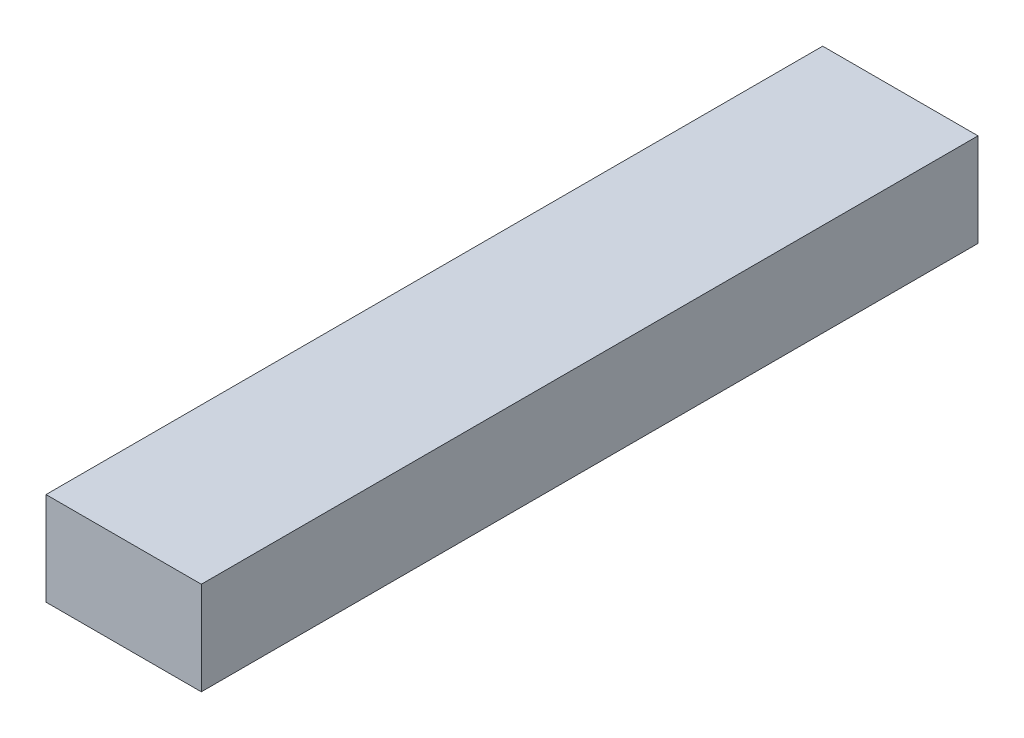
SolidWorks part; units mm, degrees
material "1060-H14"
ref_plane "Front Plane" through (0, 0, 0) normal (0, 0, 1) x (1, 0, 0)
ref_plane "Top Plane" through (0, 0, 0) normal (0, 1, 0) x (1, 0, 0)
ref_plane "Right Plane" through (0, 0, 0) normal (1, 0, 0) x (0, 0, -1)
sketch "Sketch1" plane through (0, 0, 0) normal (0, 1, 0) x (1, 0, 0)
  line L1 (-0.5, -2.5) -> (0.5, -2.5)
  line L2 (-0.5, -2.5) -> (-0.5, 2.5)
  line L3 (-0.5, 2.5) -> (0.5, 2.5)
  line L4 (0.5, -2.5) -> (0.5, 2.5)
  line L5 (-0.5, -2.5) -> (0.5, 2.5) construction
  line L6 (-0.5, 2.5) -> (0.5, -2.5) construction
  point P0 (0, 0)
  dimension "D1" = 1
  dimension "D2" = 5
extrude "Boss-Extrude1" add sketch "Sketch1" along normal mid plane 0.6
